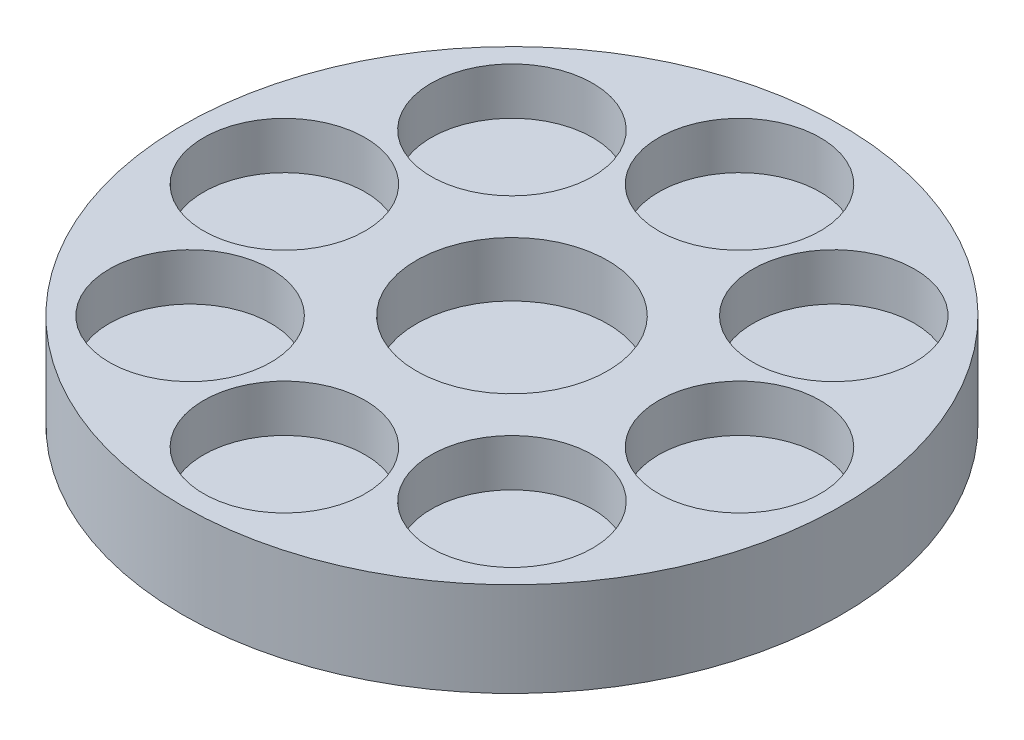
SolidWorks part; units mm, degrees
ref_plane "정면" through (0, 0, 0) normal (0, 0, 1) x (1, 0, 0)
ref_plane "윗면" through (0, 0, 0) normal (0, 1, 0) x (1, 0, 0)
ref_plane "우측면" through (0, 0, 0) normal (1, 0, 0) x (0, 0, -1)
sketch "스케치1" plane through (0, 0, 0) normal (0, 1, 0) x (1, 0, 0)
  circle A0 centre (0, 0) radius 21
  point P39 (0, 0)
  dimension "D1" = 42
extrude "보스-돌출9" add sketch "스케치1" against normal blind 6 contours A0
sketch "스케치2" plane through (0, 0, 0) normal (0, 1, 0) x (1, 0, 0)
  line L0 (0, -55) -> (0, 55) construction
  circle A0 centre (0, 14.5) radius 5.15
  dimension "D1" = 10.3
  dimension "D2" = 14.5
extrude "컷-돌출11" cut sketch "스케치2" against normal blind 3 contours A0
pattern_circular "원형 패턴4" count 8 over 360 about axis through (0, 0, 0) along (0, 1, 0) of "컷-돌출11"
sketch "스케치3" plane through (0, -6, 0) normal (0, -1, 0) x (1, 0, 0)
  line L0 (55, 0) -> (-55, 0) construction
  line L1 (5.9316, -14.3201) -> (14.3201, -5.9316)
  line L2 (14.3201, -5.9316) -> (14.3201, 5.9316)
  line L3 (14.3201, 5.9316) -> (5.9316, 14.3201)
  line L4 (5.9316, 14.3201) -> (-5.9316, 14.3201)
  line L5 (-5.9316, 14.3201) -> (-14.3201, 5.9316)
  line L6 (-14.3201, 5.9316) -> (-14.3201, -5.9316)
  line L7 (-14.3201, -5.9316) -> (-5.9316, -14.3201)
  line L8 (-5.9316, -14.3201) -> (5.9316, -14.3201)
  line L9 (6.4286, -15.5201) -> (15.5201, -6.4286)
  line L10 (15.5201, -6.4286) -> (15.5201, 6.4286)
  line L11 (15.5201, 6.4286) -> (6.4286, 15.5201)
  line L12 (6.4286, 15.5201) -> (-6.4286, 15.5201)
  line L13 (-6.4286, 15.5201) -> (-15.5201, 6.4286)
  line L14 (-15.5201, 6.4286) -> (-15.5201, -6.4286)
  line L15 (-15.5201, -6.4286) -> (-6.4286, -15.5201)
  line L16 (-6.4286, -15.5201) -> (6.4286, -15.5201)
  line L17 (5.4345, -13.1201) -> (13.1201, -5.4345)
  line L18 (13.1201, -5.4345) -> (13.1201, 5.4345)
  line L19 (13.1201, 5.4345) -> (5.4345, 13.1201)
  line L20 (5.4345, 13.1201) -> (-5.4345, 13.1201)
  line L21 (-5.4345, 13.1201) -> (-13.1201, 5.4345)
  line L22 (-13.1201, 5.4345) -> (-13.1201, -5.4345)
  line L23 (-13.1201, -5.4345) -> (-5.4345, -13.1201)
  line L24 (-5.4345, -13.1201) -> (5.4345, -13.1201)
  circle A0 centre (0, 0) radius 15.5 construction
  circle A1 centre (0, 0) radius 21 construction
  dimension "D1" = 31
  dimension "D2" = 1.2
  dimension "D3" = 1.2
extrude "컷-돌출12" cut sketch "스케치3" against normal blind 1 contours L7 L8 L1 L2 L3 L4 L5 L6 L24 L23 L22 L21 L20 L19 L18 L17
sketch "스케치4" plane through (0, 0, 0) normal (0, 1, 0) x (1, 0, 0)
  circle A0 centre (0, 0) radius 6.1
  dimension "D1" = 12.2
extrude "컷-돌출13" cut sketch "스케치4" against normal blind 3.5
sketch "스케치5" plane through (0, -6, 0) normal (0, -1, 0) x (1, 0, 0)
  circle A0 centre (0, 0) radius 3.15
  circle A1 centre (0, 0) radius 1.95
  dimension "D1" = 6.3
  dimension "D2" = 3.9
extrude "컷-돌출14" cut sketch "스케치5" against normal blind 1
sketch "스케치6" plane through (0, -6, 0) normal (0, -1, 0) x (1, 0, 0)
  circle A0 centre (0, 0) radius 3.15 construction
  circle A1 centre (0, 0) radius 3.15
  circle A2 centre (0, 0) radius 4.15
  dimension "D1" = 1
extrude "보스-돌출10" add sketch "스케치6" along normal blind 5
